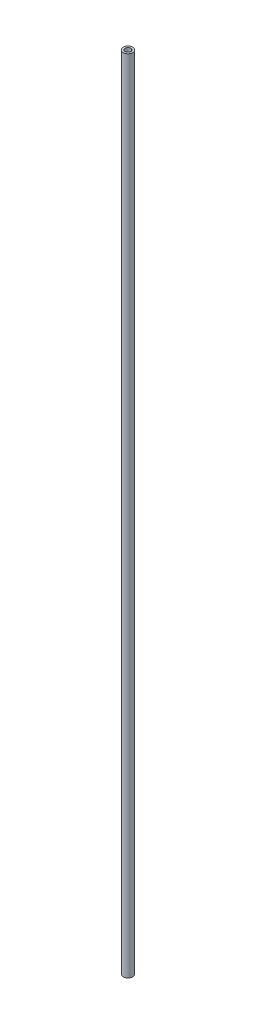
SolidWorks part; units mm, degrees
material "Thornel VCB-20 Carbon Cloth"
ref_plane "Front Plane" through (0, 0, 0) normal (0, 0, 1) x (1, 0, 0)
ref_plane "Top Plane" through (0, 0, 0) normal (0, 1, 0) x (1, 0, 0)
ref_plane "Right Plane" through (0, 0, 0) normal (1, 0, 0) x (0, 0, -1)
sketch "Sketch2" plane through (0, 0, 0) normal (0, 1, 0) x (1, 0, 0)
  circle A0 centre (0, 0) radius 2.5
  circle A1 centre (0, 0) radius 1.5
  dimension "D1" = 5
  dimension "D2" = 3
extrude "Boss-Extrude3" add sketch "Sketch2" along normal mid plane 419 contours A1 | A0
